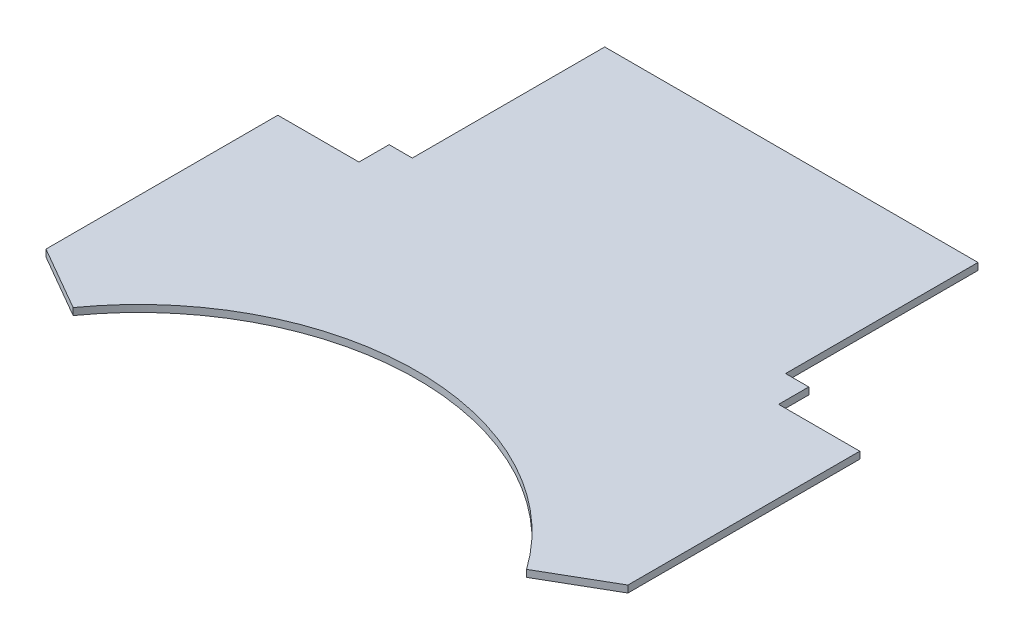
SolidWorks part; units mm, degrees
ref_plane "Face" through (0, 0, 0) normal (0, 0, 1) x (1, 0, 0)
ref_plane "Dessus" through (0, 0, 0) normal (0, 1, 0) x (1, 0, 0)
ref_plane "Droite" through (0, 0, 0) normal (1, 0, 0) x (0, 0, -1)
sketch "Esquisse1" plane through (0, 0, 0) normal (0, 1, 0) x (1, 0, 0)
  line L0 (80.5, 0) -> (-80.5, 0)
  line L1 (-80.5, 0) -> (-80.5, -83)
  line L2 (-80.5, -83) -> (-90.5, -83)
  line L3 (-90.5, -83) -> (-90.5, -96)
  line L4 (-90.5, -96) -> (-125.5, -96)
  line L5 (-125.5, -96) -> (-125.5, -196)
  line L6 (-125.5, -196) -> (-97.7872, -212)
  line L7 (0, 0) -> (0, -458.1252) construction
  line L8 (-125.5, -196) -> (-125.5, -261.7398) construction
  line L9 (125.5, -196) -> (97.7872, -212)
  line L10 (125.5, -96) -> (125.5, -196)
  line L11 (90.5, -96) -> (125.5, -96)
  line L12 (90.5, -83) -> (90.5, -96)
  line L13 (80.5, -83) -> (90.5, -83)
  line L14 (80.5, 0) -> (80.5, -83)
  arc A0 (-97.7872, -212) -> (97.7872, -212) centre (0, -281.5533) cw
  dimension "D9" = 120
  dimension "D1" = 80.5
  dimension "D2" = 83
  dimension "D3" = 10
  dimension "D4" = 13
  dimension "D5" = 35
  dimension "D6" = 60
  dimension "D7" = 32
  dimension "D8" = 100
extrude "Extrusion1" add sketch "Esquisse1" along normal blind 3
